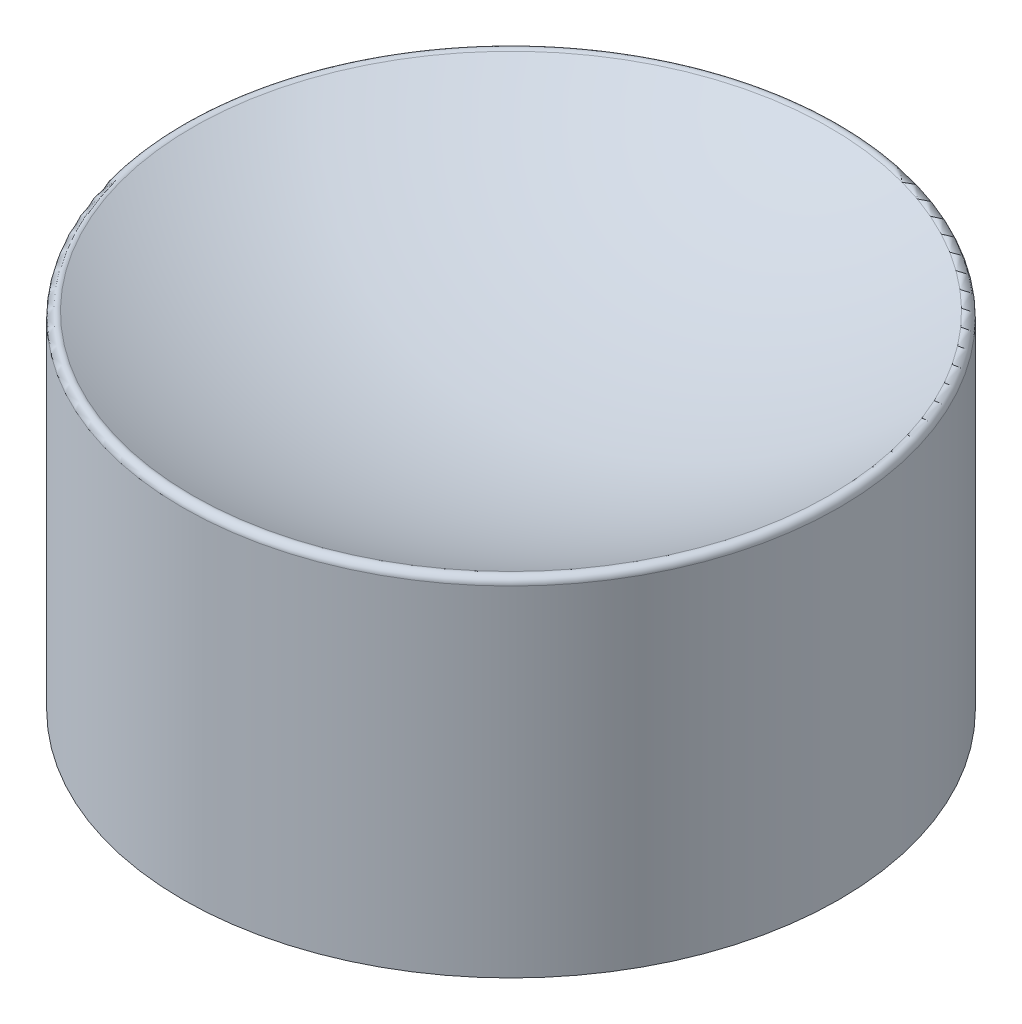
SolidWorks part; units mm, degrees
ref_plane "Front Plane" through (0, 0, 0) normal (0, 0, 1) x (1, 0, 0)
ref_plane "Top Plane" through (0, 0, 0) normal (0, 1, 0) x (1, 0, 0)
ref_plane "Right Plane" through (0, 0, 0) normal (1, 0, 0) x (0, 0, -1)
sketch "Sketch2" plane through (0, 0, 0) normal (0, 1, 0) x (1, 0, 0)
  circle A0 centre (0, 0) radius 5
  dimension "D1" = 10
extrude "Boss-Extrude1" add sketch "Sketch2" along normal blind 8
sketch "Sketch3" plane through (0, 0, 0) normal (0, 0, 1) x (1, 0, 0)
  line L0 (0, 0) -> (0, 9.7452) construction
  line L1 (5, 8) -> (-5, 8) construction
  line L2 (5, 8) -> (-5, 8)
  line L3 (0, 8) -> (0, 14) construction
  line L4 (0, 24) -> (0, 4)
  circle A0 centre (0, 14) radius 10
  dimension "D2" = 20
  dimension "D1" = 6
revolve "Cut-Revolve1" cut sketch "Sketch3" angle 360 about L4
fillet "Fillet1" radius 0.1 1 edges at (0, 5.3397, 5)
